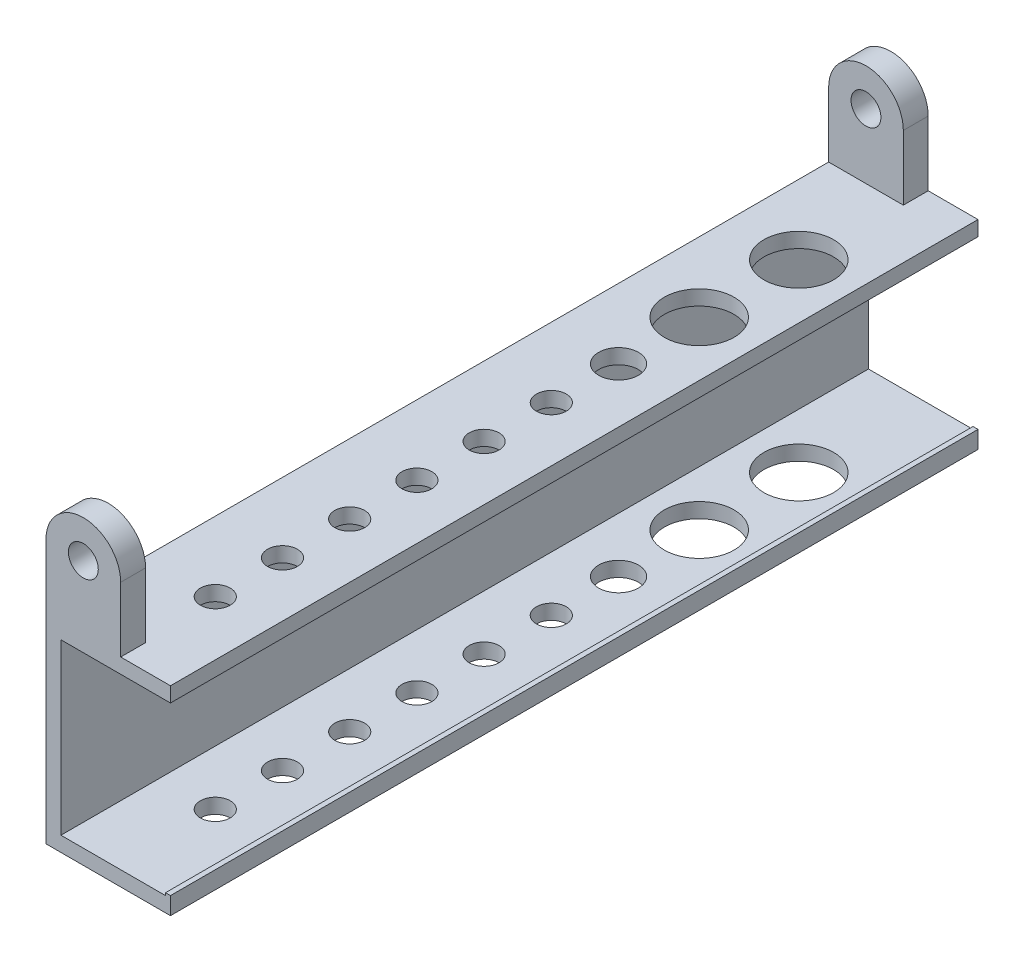
SolidWorks part; units mm, degrees
ref_plane "정면" through (0, 0, 0) normal (0, 0, 1) x (1, 0, 0)
ref_plane "윗면" through (0, 0, 0) normal (0, 1, 0) x (1, 0, 0)
ref_plane "우측면" through (0, 0, 0) normal (1, 0, 0) x (0, 0, -1)
sketch "스케치1" plane through (0, 0, 0) normal (0, 0, 1) x (1, 0, 0)
  line L0 (-127.7612, 0) -> (127.7612, 0) construction
  line L1 (0, 130.8832) -> (0, -130.8832) construction
  line L2 (0, -20) -> (25, -20)
  line L3 (25, -20) -> (25, -17)
  line L4 (25, -17) -> (3, -17)
  line L5 (3, -17) -> (3, 17)
  line L6 (3, 17) -> (25, 17)
  line L7 (25, 17) -> (25, 20)
  line L8 (25, 20) -> (0, 20)
  line L9 (0, 20) -> (0, -20)
  point P3 (0, 0)
  point P6 (0, 0)
  point P8 (0, 0)
  dimension "D1" = 3
  dimension "D2" = 25
  dimension "D3" = 25
  dimension "D4" = 3
  dimension "D5" = 3
  dimension "D6" = 40
extrude "보스-돌출1" add sketch "스케치1" along normal blind 162.2
sketch "스케치2" plane through (0, 0, 162.2) normal (0, 0, 1) x (1, 0, 0)
  line L0 (14, 31.3629) -> (14, -35.9163) construction
  line L1 (3, 17) -> (25, 17) construction
  point P4 (14, 17)
sketch "스케치3" plane through (0, 20, 0) normal (0, 1, 0) x (1, 0, 0)
  line L0 (14, -192.6339) -> (14, 7.0227) construction
  line L1 (25, -162.2) -> (25, 0) construction
  line L2 (25, -162.2) -> (0, -162.2) construction
  line L3 (25, 0) -> (0, 0) construction
  circle A0 centre (14, -142.2) radius 3
  circle A1 centre (14, -128.7) radius 3
  circle A2 centre (14, -115.2) radius 3
  circle A3 centre (14, -101.7) radius 3
  circle A4 centre (14, -74.7) radius 3
  circle A5 centre (14, -88.2) radius 3
  circle A6 centre (14, -45) radius 7
  circle A7 centre (14, -25) radius 7
  circle A8 centre (14, -61.2) radius 4
  dimension "D2" = 6
  dimension "D3" = 6
  dimension "D4" = 6
  dimension "D5" = 6
  dimension "D6" = 6
  dimension "D7" = 6
  dimension "D8" = 14
  dimension "D9" = 14
  dimension "D10" = 8
  dimension "D1" = 11
  dimension "D11" = 20
  dimension "D12" = 13.5
  dimension "D13" = 13.5
  dimension "D14" = 13.5
  dimension "D15" = 13.5
  dimension "D16" = 13.5
  dimension "D17" = 25
  dimension "D18" = 13.5
  dimension "D19" = 20
sketch "스케치4" plane through (0, 0, 162.2) normal (0, 0, 1) x (1, 0, 0)
  line L0 (0, 20) -> (15, 20)
  line L1 (0, 20) -> (15, 20)
  line L2 (0, 20) -> (0, 33)
  line L3 (0, 33) -> (15, 33)
  line L4 (15, 20) -> (15, 33)
  arc A0 (0, 33) -> (15, 33) centre (7.5, 33) cw
  circle A1 centre (7.5, 33) radius 3
  line M7 (25, 20) -> (0, 20)
  dimension "D1" = 6
  dimension "D2" = 15
  dimension "D3" = 13
extrude "보스-돌출2" add sketch "스케치4" against normal blind 5 contours A1 L3 A0 | A1 L3 L2 L4 M7
sketch "스케치5" plane through (0, 0, 0) normal (0, 0, -1) x (-1, 0, 0)
  line L1 (-15, 33) -> (0, 33)
  line L2 (-15, 33) -> (-15, 20)
  line L3 (-15, 20) -> (0, 20)
  line L4 (0, 33) -> (0, 20)
  circle A0 centre (-7.5, 33) radius 3
  arc A1 (-15, 33) -> (0, 33) centre (-7.5, 33) cw
  line M5 (0, 20) -> (-25, 20)
  dimension "D1" = 7.5
  dimension "D2" = 6
extrude "보스-돌출3" add sketch "스케치5" against normal blind 5 contours A0 L1 L2 L4 M5 | A1 L1 A0
sketch "스케치6" plane through (0, 0, 162.2) normal (0, 0, 1) x (1, 0, 0)
  line L1 (25, -17) -> (24, -17)
  line L2 (25, -17) -> (25, -16.5)
  line L3 (25, -16.5) -> (24, -16.5)
  line L4 (24, -17) -> (24, -16.5)
  dimension "D1" = 0.5
  dimension "D2" = 1
extrude "보스-돌출4" add sketch "스케치6" against normal up to vertex (162.2 mm away)
extrude "컷-돌출1" cut sketch "스케치3" against normal blind 40 contours A7
